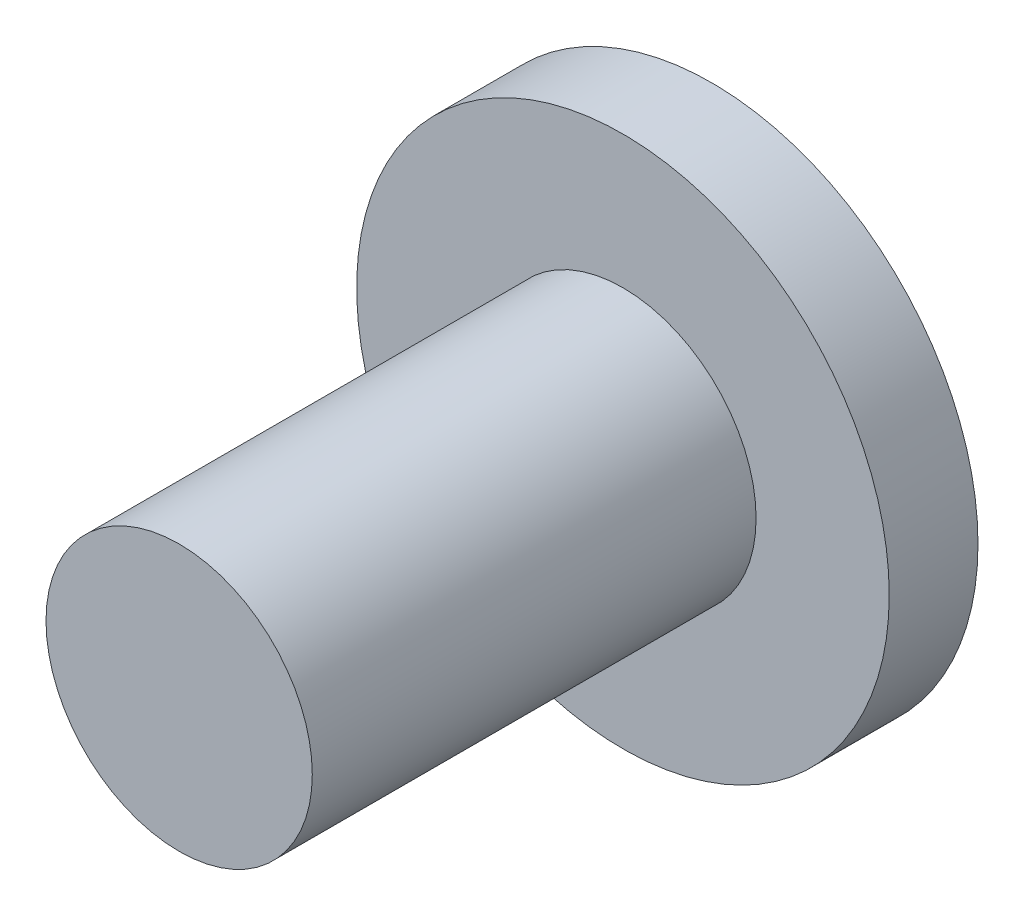
SolidWorks part; units mm, degrees
ref_plane "Front" through (0, 0, 0) normal (0, 0, 1) x (1, 0, 0)
ref_plane "Top" through (0, 0, 0) normal (0, 1, 0) x (1, 0, 0)
ref_plane "Right" through (0, 0, 0) normal (1, 0, 0) x (0, 0, -1)
sketch "Sketch1" plane through (0, 0, 0) normal (0, 0, 1) x (1, 0, 0)
  circle A0 centre (0, 0) radius 6
  dimension "D1" = 12
extrude "Boss-Extrude1" add sketch "Sketch1" along normal blind 2 contours A0
sketch "Sketch2" plane through (0, 0, 2) normal (0, 0, 1) x (1, 0, 0)
  circle A0 centre (0, 0) radius 3
  dimension "D1" = 6
extrude "Boss-Extrude2" add sketch "Sketch2" along normal blind 10
